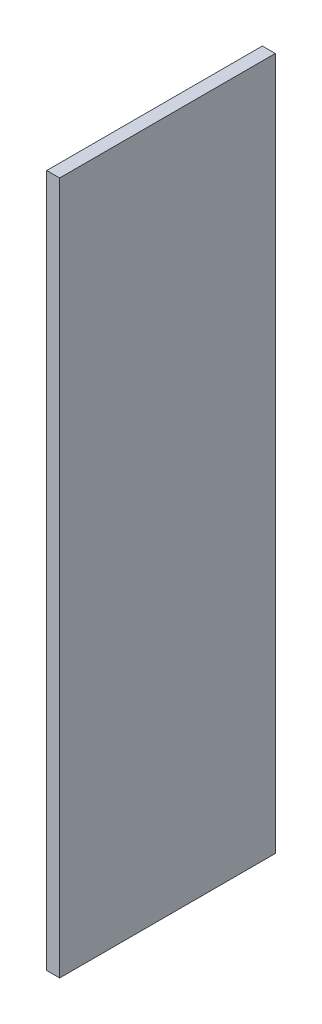
SolidWorks part; units mm, degrees
ref_plane "Front Plane" through (0, 0, 0) normal (0, 0, 1) x (1, 0, 0)
ref_plane "Top Plane" through (0, 0, 0) normal (0, 1, 0) x (1, 0, 0)
ref_plane "Right Plane" through (0, 0, 0) normal (1, 0, 0) x (0, 0, -1)
sketch "Sketch1" plane through (0, 0, 0) normal (1, 0, 0) x (0, 0, -1)
  line L1 (32.3921, -906.2196) -> (-267.6079, -906.2196)
  line L2 (32.3921, -906.2196) -> (32.3921, 57.7804)
  line L3 (32.3921, 57.7804) -> (-267.6079, 57.7804)
  line L4 (-267.6079, -906.2196) -> (-267.6079, 57.7804)
  line L5 (32.3921, -906.2196) -> (-267.6079, 57.7804) construction
  line L6 (32.3921, 57.7804) -> (-267.6079, -906.2196) construction
  point P0 (-117.6079, -424.2196)
  dimension "D1" = 300
  dimension "D2" = 964
extrude "Boss-Extrude1" add sketch "Sketch1" along normal blind 18
equation "\"H_POLKI\"=964"
equation "\"D2@Sketch1\"=\"H_POLKI\""
equation "\"DSP_WIDTH\"=18"
equation "\"D1@Boss-Extrude1\"=\"DSP_WIDTH\""
